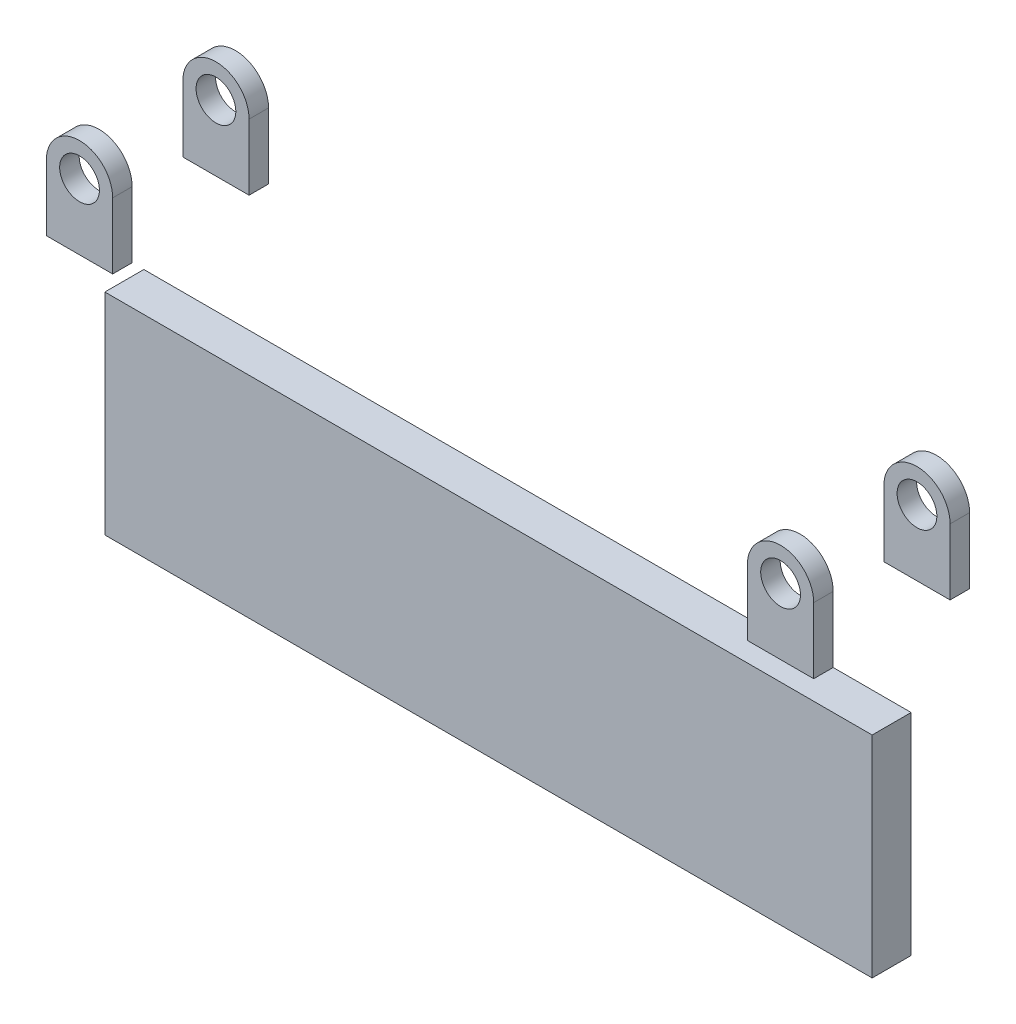
SolidWorks part; units mm, degrees
material "Plain Carbon Steel"
ref_plane "Front Plane" through (0, 0, 0) normal (0, 0, 1) x (1, 0, 0)
ref_plane "Top Plane" through (0, 0, 0) normal (0, 1, 0) x (1, 0, 0)
ref_plane "Right Plane" through (0, 0, 0) normal (1, 0, 0) x (0, 0, -1)
sketch "Sketch2" plane through (0, 0, 0) normal (0, 0, 1) x (1, 0, 0)
  line L5 (-10.795, 0) -> (-10.795, -21.4772)
  line L6 (10.795, 0) -> (10.795, -21.4772)
  line L7 (10.795, -21.4772) -> (-10.795, -21.4772)
  line L12 (217.6526, 0) -> (217.6526, -21.4772)
  line L13 (239.2426, 0) -> (239.2426, -21.4772)
  line L14 (239.2426, -21.4772) -> (217.6526, -21.4772)
  arc A0 (10.795, 0) -> (-10.795, 0) centre (0, 0) ccw
  circle A1 centre (0, 0) radius 6.477
  arc A2 (239.2426, 0) -> (217.6526, 0) centre (228.4476, 0) ccw
  circle A3 centre (228.4476, 0) radius 6.477
  dimension "D1" = 21.59
  dimension "D2" = 12.954
  dimension "D3" = 21.59
  dimension "D4" = 12.954
  dimension "D5" = 206.8576
extrude "Boss-Extrude1" add sketch "Sketch2" along normal blind 50.8
sketch "Sketch6" plane through (239.2426, 0, 0) normal (1, 0, 0) x (0, 0, -1)
  line L0 (-50.8, -21.4772) -> (0, -21.4772) construction
  line L1 (-44.45, 14.8646) -> (-6.35, 14.8646)
  line L2 (-44.45, 14.8646) -> (-44.45, -21.4772)
  line L3 (-44.45, -21.4772) -> (-6.35, -21.4772)
  line L4 (-6.35, 14.8646) -> (-6.35, -21.4772)
  line L5 (0, -21.4772) -> (0, 0) construction
  line L6 (-50.8, -21.4772) -> (-50.8, 0) construction
  dimension "D1" = 6.35
  dimension "D2" = 6.35
extrude "Cut-Extrude2" cut sketch "Sketch6" against normal blind 267.208
sketch "Sketch9" plane through (0, -21.4772, 0) normal (0, -1, 0) x (1, 0, 0)
  line L0 (-10.795, 50.8) -> (-10.795, 44.45) construction
  line L1 (-10.795, 31.75) -> (239.2426, 31.75)
  line L2 (-10.795, 31.75) -> (-10.795, 19.05)
  line L3 (-10.795, 19.05) -> (239.2426, 19.05)
  line L4 (239.2426, 31.75) -> (239.2426, 19.05)
  line L6 (239.2426, 50.8) -> (239.2426, 44.45) construction
  line L7 (-10.795, 44.45) -> (10.795, 44.45) construction
  line L8 (-10.795, 6.35) -> (10.795, 6.35) construction
  point P8 (-15.7035, 40.156)
  dimension "D1" = 0
  dimension "D2" = 0
  dimension "D3" = 12.7
  dimension "D4" = 12.7
extrude "Boss-Extrude2" add sketch "Sketch9" along normal blind 93.98 separate body
sketch "Sketch10" plane through (0, -21.4772, 0) normal (0, 1, 0) x (1, 0, 0)
  line L0 (-10.795, -19.05) -> (-10.795, -31.75)
  line L1 (-10.795, -31.75) -> (239.2426, -31.75)
  line L2 (239.2426, -31.75) -> (239.2426, -19.05)
  line L3 (239.2426, -19.05) -> (-10.795, -19.05)
extrude "Cut-Extrude3" cut sketch "Sketch10" against normal blind 25.4
